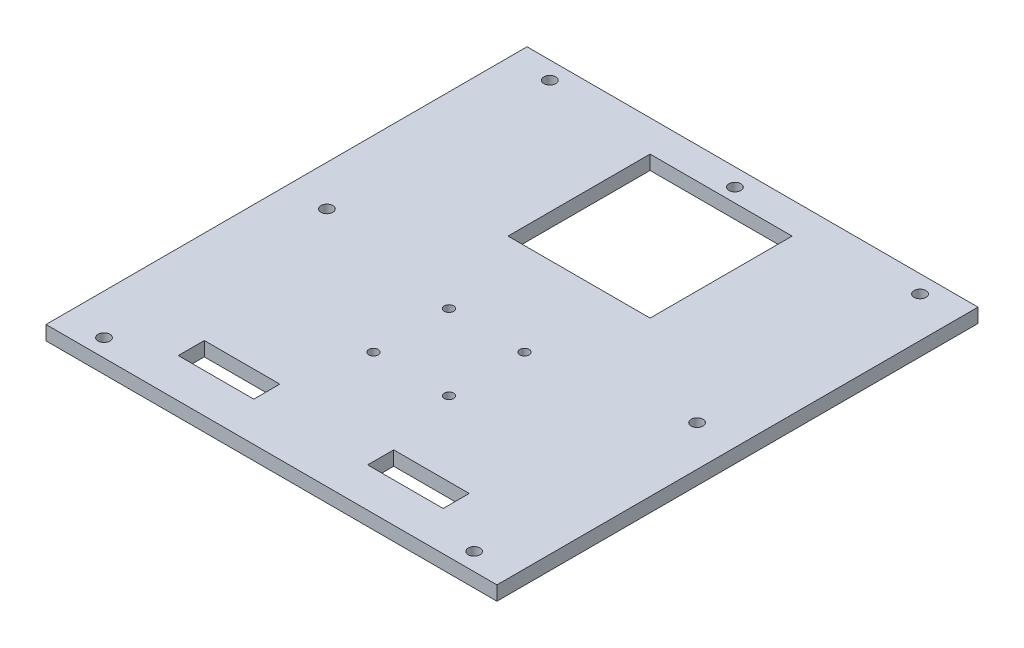
SolidWorks part; units mm, degrees
material "Acrylic (Medium-high impact)"
ref_plane "Front Plane" through (0, 0, 0) normal (0, 0, 1) x (1, 0, 0)
ref_plane "Top Plane" through (0, 0, 0) normal (0, 1, 0) x (1, 0, 0)
ref_plane "Right Plane" through (0, 0, 0) normal (1, 0, 0) x (0, 0, -1)
sketch "Sketch2" plane through (0, 0, 0) normal (0, 1, 0) x (1, 0, 0)
  line L1 (-95.25, 101.6) -> (95.25, 101.6)
  line L2 (-95.25, 101.6) -> (-95.25, -101.6)
  line L3 (-95.25, -101.6) -> (95.25, -101.6)
  line L4 (95.25, 101.6) -> (95.25, -101.6)
  line L5 (-95.25, 101.6) -> (95.25, -101.6) construction
  line L6 (-95.25, -101.6) -> (95.25, 101.6) construction
  point P0 (0, 0)
extrude "Boss-Extrude1" add sketch "Sketch2" along normal blind 6
sketch "Sketch5" plane through (0, 6, 0) normal (0, 1, 0) x (1, 0, 0)
  line L0 (-78.187, 101.6) -> (-78.187, 86.7301)
  line L1 (95.25, 101.6) -> (-95.25, 101.6) construction
  line L2 (-78.187, 94.1651) -> (-95.25, 94.1651)
  line L3 (-95.25, 101.6) -> (-95.25, -101.6) construction
  line L4 (0, 101.6) -> (0, -101.6)
  line L5 (-95.25, -101.6) -> (95.25, -101.6) construction
  line L6 (0, 0) -> (-95.25, 0)
  line L7 (0, 0) -> (95.25, 0)
  line L8 (95.25, -101.6) -> (95.25, 101.6) construction
  circle A0 centre (-78.187, 94.1651) radius 2.5
  circle A1 centre (78.187, 94.1651) radius 2.5
  circle A2 centre (-78.187, -94.1651) radius 2.5
  circle A3 centre (78.187, -94.1651) radius 2.5
  circle A4 centre (-78.187, 0) radius 2.5
  circle A5 centre (78.187, 0) radius 2.5
  circle A7 centre (0, 94.1651) radius 2.5
extrude "Cut-Extrude6" cut sketch "Sketch5" against normal through all
sketch "Sketch6" plane through (0, 6, 0) normal (0, 1, 0) x (1, 0, 0)
  line L0 (-95.25, 0) -> (95.25, 0)
  line L1 (-95.25, 101.6) -> (95.25, 101.6)
  line L2 (-95.25, 101.6) -> (-95.25, -101.6)
  line L3 (-95.25, -101.6) -> (95.25, -101.6)
  line L4 (95.25, 101.6) -> (95.25, -101.6)
  line L5 (15.95, 42.376) -> (20, 42.376)
  line L6 (-15.95, 42.376) -> (-15.95, 0)
  line L11 (-15.95, 42.376) -> (15.95, 74.276) construction
  line L12 (-15.95, 74.276) -> (15.95, 42.376) construction
  line L13 (-30, 88.326) -> (30, 88.326)
  line L14 (-30, 88.326) -> (-30, 28.326)
  line L15 (-30, 28.326) -> (30, 28.326)
  line L16 (30, 88.326) -> (30, 28.326)
  line L17 (-30, 88.326) -> (30, 28.326) construction
  line L18 (-30, 28.326) -> (30, 88.326) construction
  line L23 (-20, 78.326) -> (20, 38.326) construction
  line L24 (-20, 38.326) -> (20, 78.326) construction
  line L25 (20, 42.376) -> (20, 0)
  line L27 (20, 0) -> (40, 0)
  line L35 (55.95, 0) -> (20, 0)
  line L42 (0, -101.6) -> (0, -85.026)
  line L43 (24.05, -85.026) -> (24.05, -74.026)
  line L44 (24.05, -74.026) -> (55.95, -74.026)
  line L45 (55.95, -74.026) -> (55.95, -85.026)
  line L46 (55.95, -85.026) -> (24.05, -85.026)
  line L47 (-24.05, 0) -> (-24.05, -85.026)
  line L48 (-24.05, -85.026) -> (-24.05, -74.026)
  line L49 (-24.05, -74.026) -> (-55.95, -74.026)
  line L50 (-55.95, -74.026) -> (-55.95, -85.026)
  line L51 (-55.95, -85.026) -> (-24.05, -85.026)
  line L52 (24.05, -85.026) -> (20, -85.026)
  line L53 (20, -85.026) -> (20, -42.576)
  line L54 (20, -42.576) -> (15.95, -42.576)
  line L55 (15.95, -42.576) -> (-15.95, -42.576)
  line L56 (-15.95, -42.576) -> (-15.95, -10.676)
  line L57 (-15.95, -10.676) -> (15.95, -10.676)
  circle A4 centre (15.95, -42.576) radius 2
  circle A5 centre (-15.95, -42.576) radius 2
  circle A6 centre (-15.95, -10.676) radius 2
  circle A7 centre (15.95, -10.676) radius 2
  point P11 (0, 58.326)
  point P16 (0, 58.326)
  point P25 (0, 58.326)
  dimension "D5" = 40
  dimension "D1" = 31.9
  dimension "D2" = 31.9
  dimension "D3" = 60
  dimension "D4" = 60
  dimension "D6" = 40
  dimension "D7" = 42.45
extrude "Cut-Extrude8" cut sketch "Sketch6" against normal blind 10
